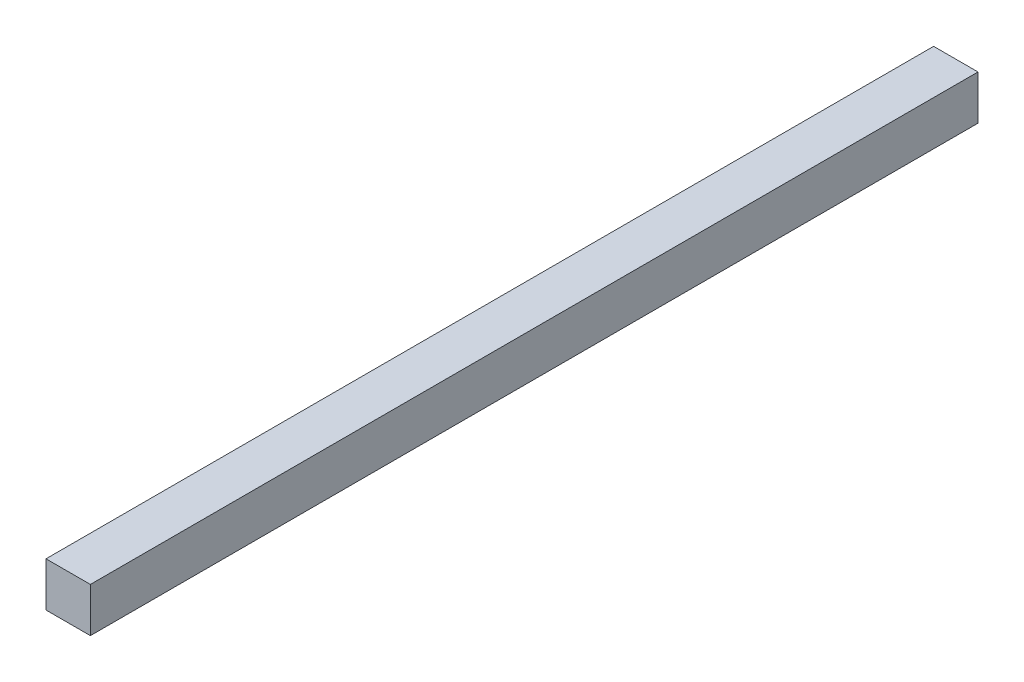
SolidWorks part; units mm, degrees
ref_plane "前视基准面" through (0, 0, 0) normal (0, 0, 1) x (1, 0, 0)
ref_plane "上视基准面" through (0, 0, 0) normal (0, 1, 0) x (1, 0, 0)
ref_plane "右视基准面" through (0, 0, 0) normal (1, 0, 0) x (0, 0, -1)
sketch "草图1" plane through (0, 0, 0) normal (0, 0, 1) x (1, 0, 0)
  line L0 (-21.8405, 23.4666) -> (-21.8405, 3.4666)
  line L1 (-21.8405, 23.4666) -> (-1.8405, 23.4666)
  line L2 (-1.8405, 3.4666) -> (-21.8405, 3.4666)
  line L3 (-1.8405, 23.4666) -> (-1.8405, 3.4666)
  dimension "D1" = 20
  dimension "D2" = 20
extrude "凸台-拉伸1" add sketch "草图1" along normal blind 400
